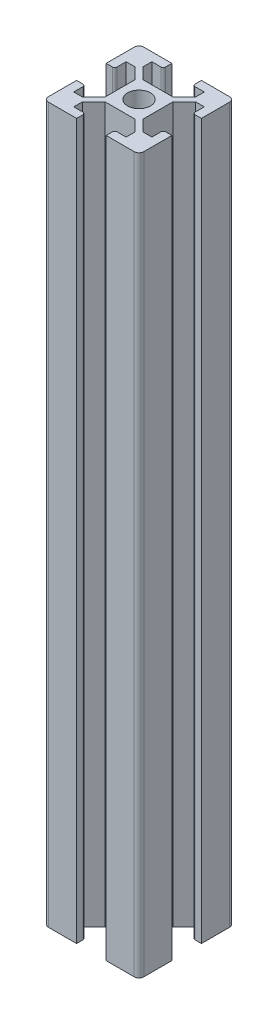
SolidWorks part; units mm, degrees
material "6063-T1"
ref_plane "Front Plane" through (0, 0, 0) normal (0, 0, 1) x (1, 0, 0)
ref_plane "Top Plane" through (0, 0, 0) normal (0, 1, 0) x (1, 0, 0)
ref_plane "Right Plane" through (0, 0, 0) normal (1, 0, 0) x (0, 0, -1)
sketch "Sketch1" plane through (0, 0, 0) normal (0, 1, 0) x (1, 0, 0)
  line L0 (0, 14.3976) -> (0, -18.4644) construction
  line L1 (-9, -10) -> (9, -10)
  line L2 (-10, -9) -> (-10, 9)
  line L3 (-9, 10) -> (9, 10)
  line L4 (10, -9) -> (10, 9)
  line L5 (-15.9976, 0) -> (13.6764, 0) construction
  line L6 (3.1, 10) -> (3.1, 8.2) construction
  line L7 (3.1, 8.2) -> (5.5, 8.2) construction
  line L8 (8.2, 5.5) -> (6.3765, 5.5) construction
  line L9 (3.1235, 4) -> (0, 4) construction
  line L10 (10, 3.1) -> (8.2, 3.1) construction
  line L11 (8.2, 3.1) -> (8.2, 5.5) construction
  line L12 (5.5, 8.2) -> (5.5, 6.3765) construction
  line L13 (4, 3.1235) -> (4, 0) construction
  line L14 (6.3765, 5.5) -> (4, 3.1235) construction
  line L15 (3.1, 10) -> (3.1, 8.7)
  line L16 (5.5, 6.3765) -> (3.1235, 4) construction
  line L17 (3.6, 8.2) -> (5.5, 8.2)
  line L18 (5.5, 8.2) -> (5.5, 6.3765)
  line L19 (5.5, 6.3765) -> (3.1235, 4)
  line L20 (3.1235, 4) -> (0, 4)
  line L21 (10, 3.1) -> (8.7, 3.1)
  line L22 (8.2, 3.6) -> (8.2, 5.5)
  line L23 (8.2, 5.5) -> (6.3765, 5.5)
  line L24 (6.3765, 5.5) -> (4, 3.1235)
  line L25 (4, 3.1235) -> (4, 0)
  line L26 (3.1, 10) -> (9, 10)
  line L27 (8.2, -5.5) -> (6.3765, -5.5)
  line L28 (8.2, -3.6) -> (8.2, -5.5)
  line L29 (10, -3.1) -> (8.7, -3.1)
  line L30 (6.3765, -5.5) -> (4, -3.1235)
  line L31 (4, -3.1235) -> (4, 0)
  line L32 (5.5, -6.3765) -> (3.1235, -4)
  line L33 (3.1235, -4) -> (0, -4)
  line L34 (5.5, -8.2) -> (5.5, -6.3765)
  line L35 (3.6, -8.2) -> (5.5, -8.2)
  line L36 (3.1, -10) -> (3.1, -8.7)
  line L37 (-5.5, -8.2) -> (-5.5, -6.3765)
  line L38 (-3.6, -8.2) -> (-5.5, -8.2)
  line L39 (-3.1, -10) -> (-3.1, -8.7)
  line L40 (-5.5, -6.3765) -> (-3.1235, -4)
  line L41 (-3.1235, -4) -> (0, -4)
  line L42 (-6.3765, -5.5) -> (-4, -3.1235)
  line L43 (-4, -3.1235) -> (-4, 0)
  line L44 (-8.2, -5.5) -> (-6.3765, -5.5)
  line L45 (-8.2, -3.6) -> (-8.2, -5.5)
  line L46 (-10, -3.1) -> (-8.7, -3.1)
  line L47 (-8.2, 5.5) -> (-6.3765, 5.5)
  line L48 (-8.2, 3.6) -> (-8.2, 5.5)
  line L49 (-10, 3.1) -> (-8.7, 3.1)
  line L50 (-6.3765, 5.5) -> (-4, 3.1235)
  line L51 (-4, 3.1235) -> (-4, 0)
  line L52 (-5.5, 6.3765) -> (-3.1235, 4)
  line L53 (-3.1235, 4) -> (0, 4)
  line L54 (-5.5, 8.2) -> (-5.5, 6.3765)
  line L55 (-3.6, 8.2) -> (-5.5, 8.2)
  line L56 (-3.1, 10) -> (-3.1, 8.7)
  circle A0 centre (0, 0) radius 2.4
  arc A1 (9, 10) -> (10, 9) centre (9, 9) cw
  arc A2 (9, -10) -> (10, -9) centre (9, -9) ccw
  arc A3 (-9, -10) -> (-10, -9) centre (-9, -9) cw
  arc A4 (-10, 9) -> (-9, 10) centre (-9, 9) cw
  arc A5 (8.7, 3.1) -> (8.2, 3.6) centre (8.7, 3.6) cw
  arc A6 (3.1, 8.7) -> (3.6, 8.2) centre (3.6, 8.7) ccw
  arc A7 (8.7, -3.1) -> (8.2, -3.6) centre (8.7, -3.6) ccw
  arc A8 (3.1, -8.7) -> (3.6, -8.2) centre (3.6, -8.7) cw
  arc A9 (-3.1, -8.7) -> (-3.6, -8.2) centre (-3.6, -8.7) ccw
  arc A10 (-8.7, -3.1) -> (-8.2, -3.6) centre (-8.7, -3.6) cw
  arc A11 (-8.7, 3.1) -> (-8.2, 3.6) centre (-8.7, 3.6) ccw
  arc A12 (-3.1, 8.7) -> (-3.6, 8.2) centre (-3.6, 8.7) cw
  point P0 (0, 0)
  point P10 (10, 10)
  point P13 (10, -10)
  point P18 (-10, 10)
  point P92 (0, 0)
  dimension "D5" = 4.8
  dimension "D6" = 1
  dimension "D17" = 0.5
  dimension "D1" = 20
  dimension "D2" = 20
  dimension "D3" = 10
  dimension "D4" = 10
  dimension "D7" = 1.8
  dimension "D8" = 1.8
  dimension "D9" = 3.1
  dimension "D10" = 3.1
  dimension "D11" = 5.5
  dimension "D12" = 4
  dimension "D13" = 5.5
  dimension "D14" = 4
  dimension "D15" = 4.2
  dimension "D16" = 45
  dimension "D18" = 3.1235
  dimension "D19" = 4
extrude "Boss-Extrude1" add sketch "Sketch1" along normal blind 150 contours A12 L56 L3 A4 L2 L49 A11 L48 L47 L50 L51 L43 L42 L44 L45 A10 L46 A3 L1 L39 A9 L38 L37 L40 L41 L33 L32 L34 L35 A8 L36 A2 L4 L29 A7 L28 L27 L30 L31 L25 L24 L23 L22 A5 L21 A1 L15
